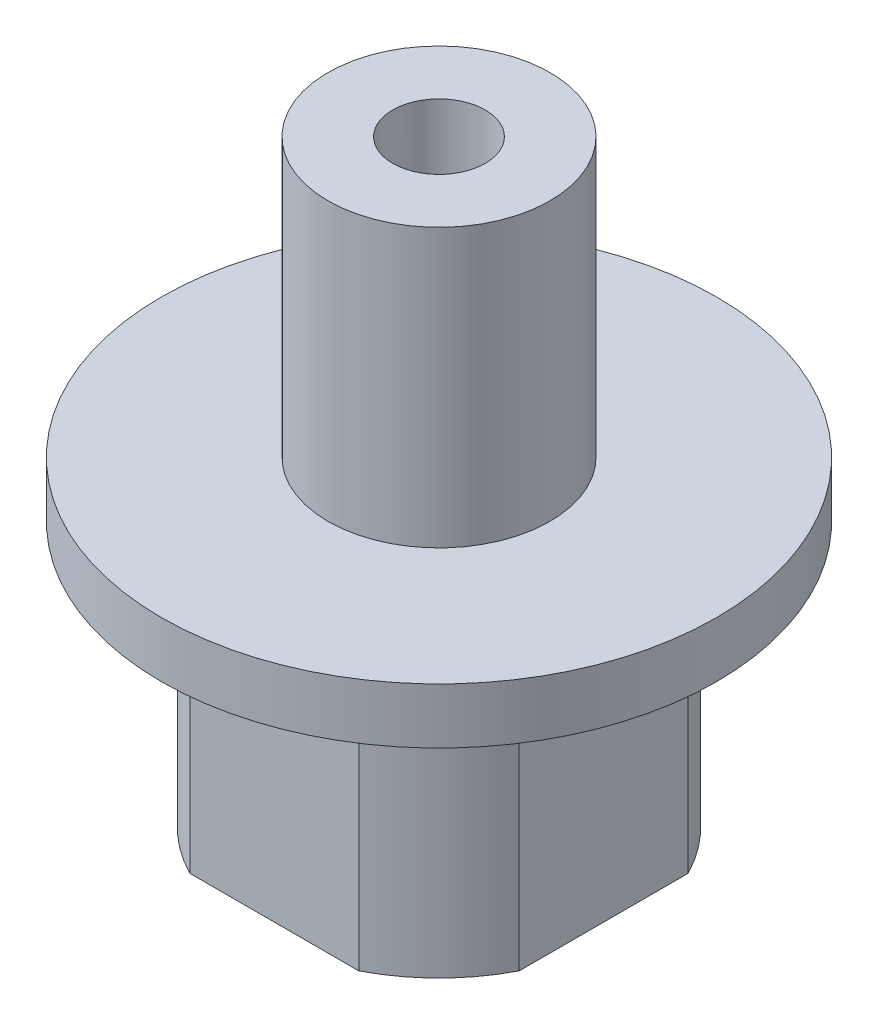
SolidWorks part; units mm, degrees
ref_plane "Front Plane" through (0, 0, 0) normal (0, 0, 1) x (1, 0, 0)
ref_plane "Top Plane" through (0, 0, 0) normal (0, 1, 0) x (1, 0, 0)
ref_plane "Right Plane" through (0, 0, 0) normal (1, 0, 0) x (0, 0, -1)
sketch "Sketch1" plane through (0, 0, 0) normal (0, 1, 0) x (1, 0, 0)
  circle A0 centre (0, 0) radius 5
  circle A1 centre (0, 0) radius 2
  dimension "D1" = 4
  dimension "D2" = 10
extrude "Boss-Extrude1" add sketch "Sketch1" along normal mid plane 7.15
sketch "Sketch2" plane through (0, 3.575, 0) normal (0, 1, 0) x (1, 0, 0)
  circle A0 centre (0, 0) radius 7.5
  circle A1 centre (0, 0) radius 2
  dimension "D1" = 15
extrude "Boss-Extrude2" add sketch "Sketch2" along normal blind 1.5
sketch "Sketch3" plane through (0, -3.575, 0) normal (0, -1, 0) x (1, 0, 0)
  line L1 (-4.449, -4.449) -> (4.449, -4.449)
  line L2 (-4.449, -4.449) -> (-4.449, 4.449)
  line L3 (-4.449, 4.449) -> (4.449, 4.449)
  line L4 (4.449, -4.449) -> (4.449, 4.449)
  line L5 (-4.449, -4.449) -> (4.449, 4.449) construction
  line L6 (-4.449, 4.449) -> (4.449, -4.449) construction
  line L7 (5.6349, -6.2206) -> (-5.6349, -6.2206)
  line L8 (5.6349, -6.2206) -> (5.6349, 6.2206)
  line L9 (5.6349, 6.2206) -> (-5.6349, 6.2206)
  line L10 (-5.6349, -6.2206) -> (-5.6349, 6.2206)
  line L11 (5.6349, -6.2206) -> (-5.6349, 6.2206) construction
  line L12 (5.6349, 6.2206) -> (-5.6349, -6.2206) construction
  point P0 (0, 0)
  point P7 (0, 0)
extrude "Cut-Extrude1" cut sketch "Sketch3" against normal up to surface (7.15 mm away) up to face at (0, 3.575, 5)
sketch "Sketch8" plane through (0, 0, -4.449) normal (0, 0, -1) x (-1, 0, 0)
  line L0 (2.2817, -3.575) -> (-2.2817, -3.575) construction
  point P0 (0, -0.575)
  dimension "D1" = 3
hole_wizard "M3x0.5 Tapped Hole1" positions "Sketch8" profile "Sketch7" tap size "M3x0.5" standard "ANSI Metric"
sketch "Sketch7" plane through (0, -0.575, -4.449) normal (1, 0, 0) x (0, 1, 0)
  line L0 (0, 0) -> (0, 2.449)
  line L1 (0, 2.449) -> (1.25, 2.449)
  line L2 (1.25, 2.449) -> (1.25, 0)
  line L5 (1.25, 0) -> (0, 0)
  line L11 (0, -6.35) -> (0, 107.95) construction
  dimension "Thru Tap Drill Dia." = 2.5
  dimension "Thru Tap Drill Depth" = 2.449
cosmetic thread "Hole Thread2" parameters "D2"=3
sketch "Sketch9" plane through (0, 5.075, 0) normal (0, 1, 0) x (1, 0, 0)
  circle A0 centre (0, 0) radius 3
  circle A1 centre (0, 0) radius 2
  circle A2 centre (0, 0) radius 2 construction
  dimension "D1" = 6
extrude "Boss-Extrude3" add sketch "Sketch9" along normal blind 7.5
sketch "Sketch11" plane through (0, 12.575, 0) normal (0, 1, 0) x (1, 0, 0)
  circle A0 centre (0, 0) radius 2
extrude "Boss-Extrude4" add sketch "Sketch11" against normal up to surface (7.5 mm away) up to face at (0, 5.075, 7.5)
sketch "Sketch14" plane through (0, 12.575, 0) normal (0, 1, 0) x (1, 0, 0)
  point P0 (0, 0)
hole_wizard "M3x0.5 Tapped Hole2" positions "Sketch14" profile "Sketch13" tap size "M3x0.5" standard "ANSI Metric" end condition up to next
sketch "Sketch13" plane through (0, 12.575, 0) normal (1, 0, 0) x (0, 0, 1)
  line L0 (0, 0) -> (0, 7.5)
  line L1 (0, 7.5) -> (1.25, 7.5)
  line L2 (1.25, 7.5) -> (1.25, 0)
  line L5 (1.25, 0) -> (0, 0)
  line L11 (0, -6.35) -> (0, 107.95) construction
  dimension "Thru Tap Drill Dia." = 2.5
  dimension "Thru Tap Drill Depth" = 7.5
cosmetic thread "Hole Thread3" parameters "D2"=3
sketch "Sketch15" plane through (0, 5.075, 0) normal (0, -1, 0) x (1, 0, 0)
  circle A0 centre (0, 0) radius 1.25
  circle A1 centre (0, 0) radius 2
extrude "Cut-Extrude2" cut sketch "Sketch15" against normal blind 2
